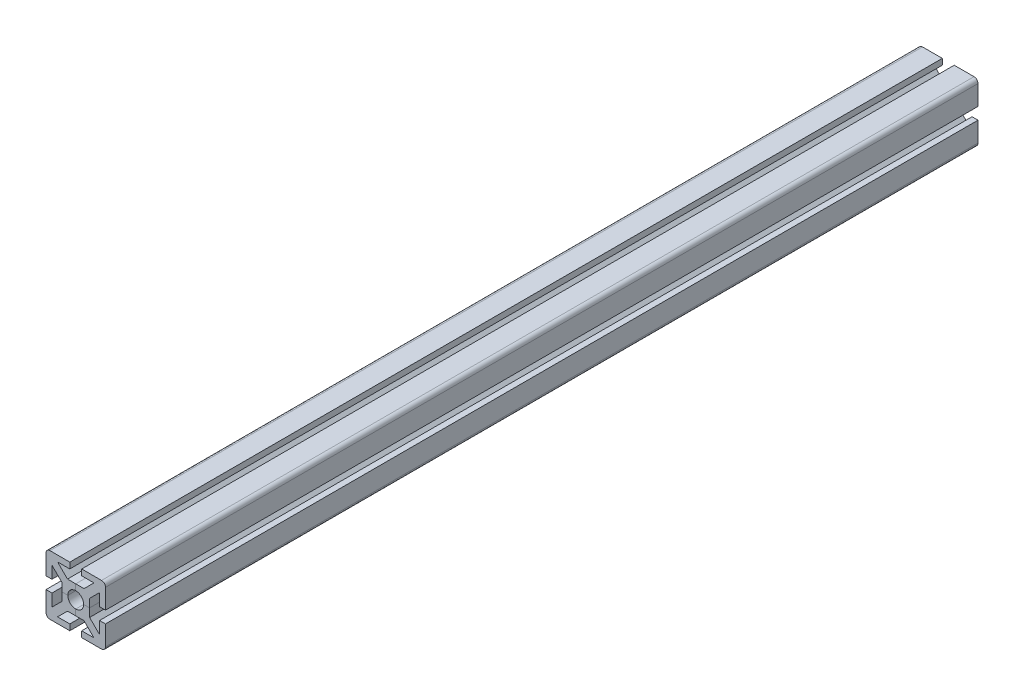
SolidWorks part; units mm, degrees
ref_plane "Alzado" through (0, 0, 0) normal (0, 0, 1) x (1, 0, 0)
ref_plane "Planta" through (0, 0, 0) normal (0, 1, 0) x (1, 0, 0)
ref_plane "Vista lateral" through (0, 0, 0) normal (1, 0, 0) x (0, 0, -1)
sketch "Croquis1" plane through (0, 0, 0) normal (0, 0, 1) x (1, 0, 0)
  line L0 (0, 0) -> (50000, 0) construction
  line L1 (-15, 15) -> (15, 15) construction
  line L2 (-15, 15) -> (-15, -15) construction
  line L3 (-15, -15) -> (15, -15) construction
  line L4 (15, 15) -> (15, -15) construction
  line L5 (-15, 15) -> (15, -15) construction
  line L6 (-15, -15) -> (15, 15) construction
  line L7 (0, 0) -> (0, -50000) construction
  line L8 (0, 4) -> (0, 7)
  line L9 (0, 7) -> (4.1716, 7)
  line L10 (4.1716, 7) -> (9.1716, 12)
  line L11 (9.1716, 12) -> (3, 12)
  line L12 (3, 12) -> (3, 15)
  line L13 (3, 15) -> (15, 15)
  line L20 (2.8284, 2.8284) -> (15, 15)
  arc A0 (2.8284, 2.8284) -> (0, 4) centre (0, 0) ccw
  point P0 (0, 0)
  dimension "D3" = 4
  dimension "D1" = 30
  dimension "D2" = 6
  dimension "D4" = 8
  dimension "D5" = 3
  dimension "D6" = 2
extrude "Saliente-Extruir1" add sketch "Croquis1" along normal mid plane 440
mirror "Simetría1" about plane through (2.8284, 2.8284, 220) normal (-0.7071, 0.7071, 0) of "Saliente-Extruir1"
fillet "Redondeo1" radius 2 1 edges at (15, 15, 0)
pattern_circular "MatrizC4" count 4 over 360 about axis through (0, 0, 0) along (0, 0, 1) of bodies 102
